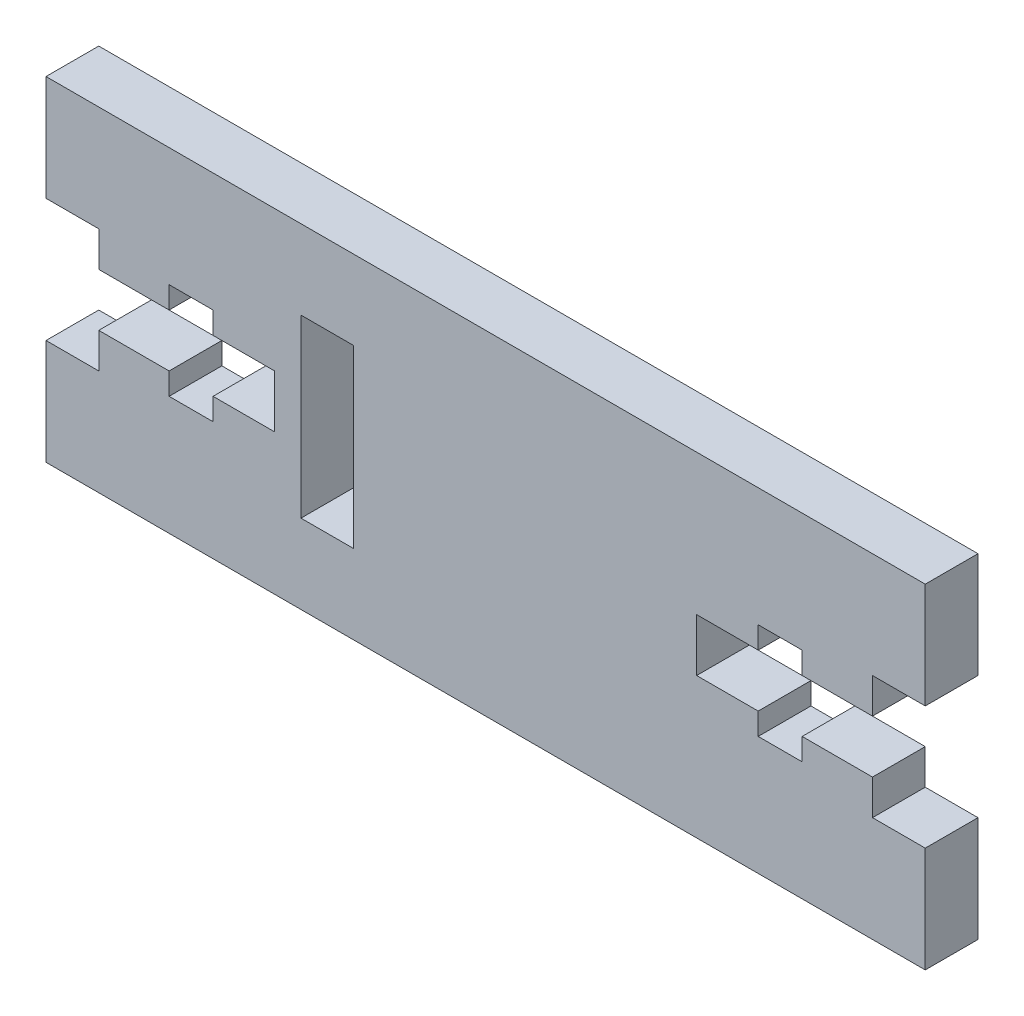
SolidWorks part; units mm, degrees
ref_plane "Front Plane" through (0, 0, 0) normal (0, 0, 1) x (1, 0, 0)
ref_plane "Top Plane" through (0, 0, 0) normal (0, 1, 0) x (1, 0, 0)
ref_plane "Right Plane" through (0, 0, 0) normal (1, 0, 0) x (0, 0, -1)
sketch "Model" plane through (0, 0, 0) normal (0, 0, 1) x (1, 0, 0)
  line L0 (83, 32.5) -> (33, 32.5)
  line L1 (83, 51.5) -> (33, 51.5)
  line L2 (46, 43.5) -> (42.5, 43.5)
  line L3 (46, 40.5) -> (42.5, 40.5)
  line L4 (42.5, 39.25) -> (40, 39.25)
  line L5 (40, 40.5) -> (36, 40.5)
  line L6 (40, 43.5) -> (36, 43.5)
  line L7 (40, 44.75) -> (42.5, 44.75)
  line L8 (36, 45.5) -> (33, 45.5)
  line L9 (36, 38.5) -> (33, 38.5)
  line L10 (36, 38.5) -> (36, 40.5)
  line L11 (36, 45.5) -> (36, 43.5)
  line L12 (40, 44.75) -> (40, 43.5)
  line L13 (40, 40.5) -> (40, 39.25)
  line L14 (42.5, 39.25) -> (42.5, 40.5)
  line L15 (46, 40.5) -> (46, 43.5)
  line L16 (42.5, 43.5) -> (42.5, 44.75)
  line L17 (47.5, 47) -> (47.5, 37)
  line L18 (50.5, 37) -> (50.5, 47)
  line L19 (50.5, 47) -> (47.5, 47)
  line L20 (50.5, 37) -> (47.5, 37)
  line L21 (70, 43.5) -> (73.5, 43.5)
  line L22 (73.5, 44.75) -> (76, 44.75)
  line L23 (76, 43.5) -> (80, 43.5)
  line L24 (80, 45.5) -> (83, 45.5)
  line L25 (83, 38.5) -> (80, 38.5)
  line L26 (80, 40.5) -> (76, 40.5)
  line L27 (76, 39.25) -> (73.5, 39.25)
  line L28 (73.5, 40.5) -> (70, 40.5)
  line L29 (70, 40.5) -> (70, 43.5)
  line L30 (73.5, 43.5) -> (73.5, 44.75)
  line L31 (73.5, 40.5) -> (73.5, 39.25)
  line L32 (76, 40.5) -> (76, 39.25)
  line L33 (76, 44.75) -> (76, 43.5)
  line L34 (80, 43.5) -> (80, 45.5)
  line L35 (80, 40.5) -> (80, 38.5)
  line L36 (83, 38.5) -> (83, 32.5)
  line L37 (83, 45.5) -> (83, 51.5)
  line L38 (33, 51.5) -> (33, 45.5)
  line L39 (33, 38.5) -> (33, 32.5)
extrude "Boss-Extrude1" add sketch "Model" along normal blind 3
